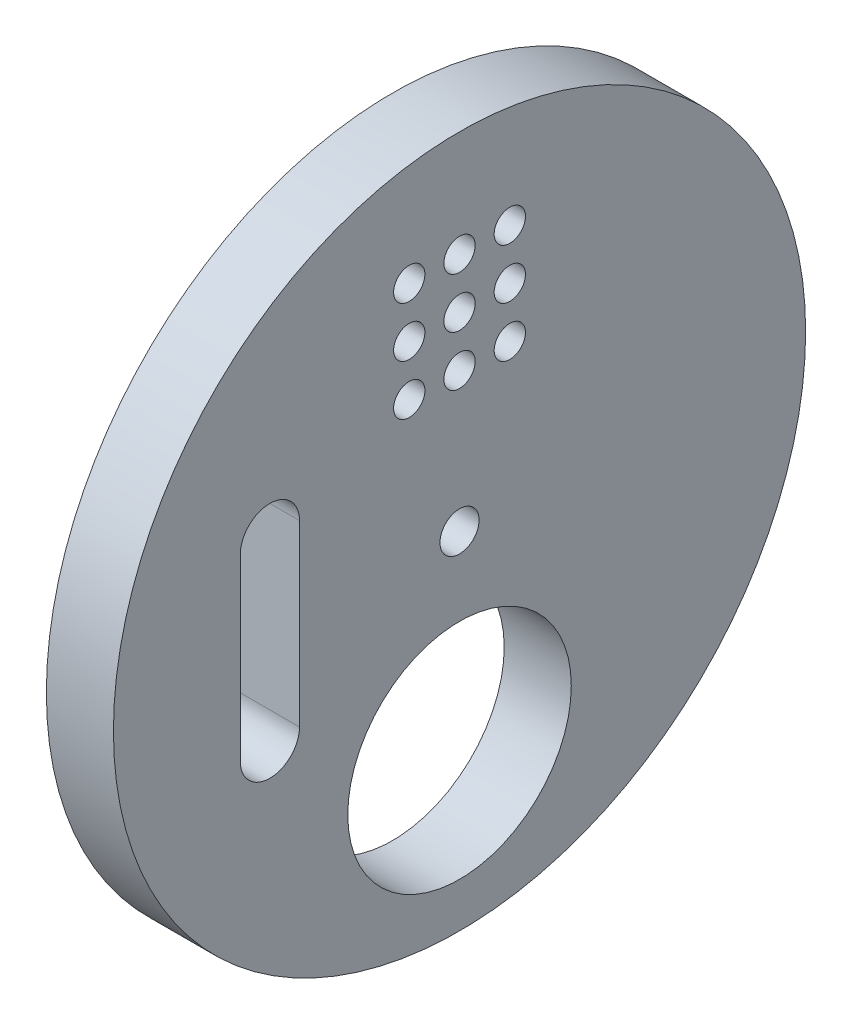
SolidWorks part; units mm, degrees
ref_plane "Front Plane" through (0, 0, 0) normal (0, 0, 1) x (1, 0, 0)
ref_plane "Top Plane" through (0, 0, 0) normal (0, 1, 0) x (1, 0, 0)
ref_plane "Right Plane" through (0, 0, 0) normal (1, 0, 0) x (0, 0, -1)
sketch "Sketch1" plane through (0, 0, 0) normal (1, 0, 0) x (0, 0, -1)
  line L1 (-56.25, -119) -> (56.25, -119)
  line L2 (-56.25, -119) -> (-56.25, 119)
  line L3 (-56.25, 119) -> (56.25, 119)
  line L4 (56.25, -119) -> (56.25, 119)
  line L5 (-56.25, -119) -> (56.25, 119) construction
  line L6 (-56.25, 119) -> (56.25, -119) construction
  point P0 (0, 0)
  dimension "D1" = 238
  dimension "D2" = 112.5
extrude "Boss-Extrude1" add sketch "Sketch1" along normal blind 6
sketch "Sketch2" plane through (6, 0, 0) normal (1, 0, 0) x (0, 0, -1)
  line L0 (0, -119) -> (0, -99) construction
  line L1 (0, -82.0294) -> (30.9706, -113) construction
  line L4 (56.25, -119) -> (56.25, 119)
  line L5 (56.25, 119) -> (-56.25, 119)
  line L6 (-56.25, 119) -> (-56.25, -119)
  line L7 (-56.25, -119) -> (56.25, -119)
  line L8 (56.25, -119) -> (56.25, 119) construction
  line L9 (56.25, 119) -> (-56.25, 119) construction
  line L10 (-56.25, 119) -> (-56.25, -119) construction
  line L11 (-56.25, -119) -> (56.25, -119) construction
  line L12 (0, -99) -> (0, -82.0294) construction
  line L13 (30.9706, -113) -> (0, -113) construction
  line L14 (0, -82.0294) -> (30.9706, -82.0294) construction
  line L15 (30.9706, -82.0294) -> (30.9706, -113) construction
  line L16 (0, -113) -> (0, -109) construction
  line L17 (8.4853, -90.5147) -> (7.0711, -91.9289) construction
  line L18 (0, -82.0294) -> (-16.9706, -82.0294) construction
  line L19 (-16.9706, -82.0294) -> (0, -65.0589) construction
  line L20 (0, -65.0589) -> (0, -82.0294) construction
  line L21 (0, -65.0589) -> (16.9706, -82.0294) construction
  line L22 (16.9706, -82.0294) -> (0, -99) construction
  line L23 (0, -99) -> (-16.9706, -82.0294) construction
  line L24 (-16.9706, -74.0294) -> (-16.9706, -90.0294) construction
  line L25 (-14.3206, -74.0294) -> (-14.3206, -90.0294)
  line L26 (-19.6206, -74.0294) -> (-19.6206, -90.0294)
  line L27 (0, -65.0589) -> (0, -60.5589) construction
  line L28 (0, -60.5589) -> (-4.5, -60.5589) construction
  line L29 (-4.5, -60.5589) -> (-4.5, -65.0589) construction
  circle A2 centre (0, -82.0294) radius 30.9706
  circle A3 centre (0, -99) radius 10
  circle A4 centre (-16.9706, -82.0294) radius 10 construction
  circle A5 centre (0, -65.0589) radius 10 construction
  arc A7 (-14.3206, -74.0294) -> (-19.6206, -74.0294) centre (-16.9706, -74.0294) ccw
  arc A8 (-19.6206, -90.0294) -> (-14.3206, -90.0294) centre (-16.9706, -90.0294) ccw
  circle A10 centre (-4.5, -60.5589) radius 1.4
  circle A11 centre (0, -60.5589) radius 1.4
  circle A12 centre (4.5, -60.5589) radius 1.4
  circle A15 centre (0, -65.0589) radius 1.4
  circle A16 centre (4.5, -65.0589) radius 1.4
  circle A19 centre (0, -69.5589) radius 1.4
  circle A20 centre (4.5, -69.5589) radius 1.4
  circle A31 centre (-4.5, -65.0589) radius 1.4
  circle A32 centre (-4.5, -69.5589) radius 1.4
  circle A35 centre (0, -82.0294) radius 1.75
  point P19 (-16.9706, -82.0294)
  dimension "D2" = 20
  dimension "D8" = 2.8
  dimension "D12" = 4.5
  dimension "D14" = 3.5
  dimension "D3" = 6
  dimension "D4" = 2
  dimension "D5" = 4
  dimension "D6" = 5.3
  dimension "D7" = 16
  dimension "D9" = 4.5
  dimension "D13" = 4.5
  dimension "D1" = 0
  dimension "D10" = 3
  dimension "D11" = 3
extrude "Boss-Extrude2" add sketch "Sketch2" along normal blind 6
sketch "Sketch3" plane through (0, 0, 0) normal (-1, 0, 0) x (0, 0, 1)
  line L4 (-56.25, 119) -> (-56.25, -119)
  line L5 (-56.25, -119) -> (56.25, -119)
  line L6 (56.25, -119) -> (56.25, 119)
  line L7 (56.25, 119) -> (-56.25, 119)
  line L8 (-56.25, 119) -> (-56.25, -119)
  line L9 (-56.25, -119) -> (56.25, -119)
  line L10 (56.25, -119) -> (56.25, 119)
  line L11 (56.25, 119) -> (-56.25, 119)
  dimension "D1" = 0
extrude "Cut-Extrude1" cut sketch "Sketch3" against normal blind 6
